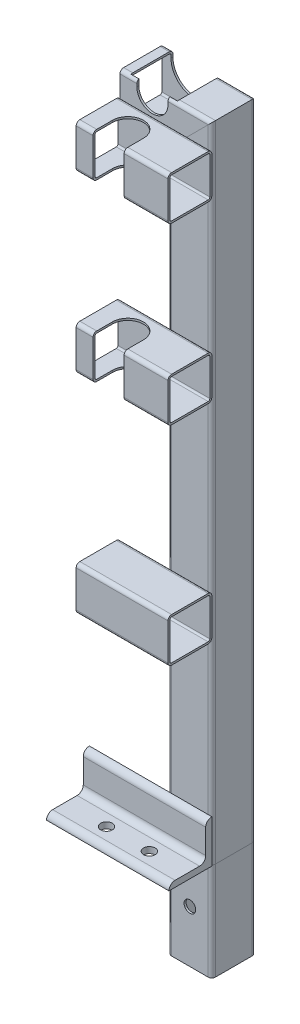
SolidWorks part; units mm, degrees
ref_plane "Front Plane" through (0, 0, 0) normal (0, 0, 1) x (1, 0, 0)
ref_plane "Top Plane" through (0, 0, 0) normal (0, 1, 0) x (1, 0, 0)
ref_plane "Right Plane" through (0, 0, 0) normal (1, 0, 0) x (0, 0, -1)
sketch "Sketch1" plane through (0, 0, 0) normal (0, 0, 1) x (1, 0, 0)
  line L0 (210.6, 0) -> (210.6, 508)
  line L1 (210.6, 508) -> (153.5, 508)
  line L2 (210.6, 0) -> (210.6, -80)
  dimension "D1" = 508
  dimension "D2" = 80
  dimension "D3" = 57.1
  dimension "D4" = 210.6
other "Structural MemberMain"
ref_plane "Plane1" through (210.6, 0, 0) normal (0, 1, 0) x (-1, 0, 0)
sketch "Sketch11" plane through (210.6, 0, 0) normal (0, 1, 0) x (-1, 0, 0)
  line L0 (-14.9, 16.3) -> (14.9, 16.3)
  line L1 (-14.9, 17.9) -> (14.9, 17.9)
  line L2 (-17.9, 14.9) -> (-17.9, -14.9)
  line L3 (-14.9, -17.9) -> (14.9, -17.9)
  line L4 (17.9, 14.9) -> (17.9, -14.9)
  line L5 (-17.9, 17.9) -> (17.9, -17.9) construction
  line L6 (-17.9, -17.9) -> (17.9, 17.9) construction
  line L7 (16.3, 14.9) -> (16.3, -14.9)
  line L8 (-14.9, -16.3) -> (14.9, -16.3)
  line L9 (-16.3, 14.9) -> (-16.3, -14.9)
  arc A0 (-17.9, -14.9) -> (-14.9, -17.9) centre (-14.9, -14.9) ccw
  arc A1 (14.9, -17.9) -> (17.9, -14.9) centre (14.9, -14.9) ccw
  arc A2 (17.9, 14.9) -> (14.9, 17.9) centre (14.9, 14.9) ccw
  arc A3 (-14.9, 17.9) -> (-17.9, 14.9) centre (-14.9, 14.9) ccw
  arc A4 (16.3, 14.9) -> (14.9, 16.3) centre (14.9, 14.9) ccw
  arc A5 (14.9, -16.3) -> (16.3, -14.9) centre (14.9, -14.9) ccw
  arc A6 (-16.3, -14.9) -> (-14.9, -16.3) centre (-14.9, -14.9) ccw
  arc A7 (-14.9, 16.3) -> (-16.3, 14.9) centre (-14.9, 14.9) ccw
  point P0 (0, 0)
  point P30 (0, 0)
  dimension "D3" = 3
  dimension "D1" = 35.8
  dimension "D2" = 35.8
  dimension "D4" = 1.6
sketch "Sketch12" plane through (0, 0, 0) normal (0, 0, 1) x (1, 0, 0)
  line L1 (180, 520.7) -> (180, 531.1) construction
  line L2 (167.3, 520.7) -> (167.3, 531.1)
  line L3 (192.7, 520.7) -> (192.7, 531.1)
  line L4 (210.6, 508) -> (153.5, 508) construction
  line L5 (153.5, 525.9) -> (228.5, 525.9) construction
  arc A0 (167.3, 520.7) -> (192.7, 520.7) centre (180, 520.7) ccw
  arc A1 (192.7, 531.1) -> (167.3, 531.1) centre (180, 531.1) ccw
  point P2 (180, 525.9)
  dimension "D1" = 25.4
  dimension "D2" = 180
extrude "Cut-ExtrudeTopRailGuide" cut sketch "Sketch12" against normal through all and the other way through all
sketch "Sketch13" plane through (0, 0, 0) normal (0, 1, 0) x (1, 0, 0)
  line L0 (128.5, -17.9) -> (228.5, -17.9)
  line L1 (192.7, -17.9) -> (225.5, -17.9) construction
  line L3 (228.5, 14.9) -> (228.5, -14.9) construction
  point P4 (178.5, -17.9)
  dimension "D1" = 100
other "Structural MemberAngle"
ref_plane "Plane2" through (128.5, 0, 17.9) normal (1, 0, 0) x (0, 1, 0)
sketch "Sketch14" plane through (128.5, 0, 17.9) normal (1, 0, 0) x (0, 1, 0)
  line L0 (0, 0) -> (0, 35)
  line L1 (0, 17.5) -> (5, 17.5) construction
  line L2 (5, 30) -> (5, 10)
  line L3 (10, 5) -> (30, 5)
  line L4 (17.5, 5) -> (17.5, 0) construction
  line L5 (35, 0) -> (0, 0)
  arc A0 (35, 0) -> (30, 5) centre (30, 0) ccw
  arc A1 (0, 35) -> (5, 30) centre (0, 30) cw
  arc A2 (10, 5) -> (5, 10) centre (10, 10) cw
  point P10 (17.5, 0)
  point P14 (0, 17.5)
  point P15 (5, 17.5)
  point P16 (17.5, 5)
  point P17 (5, 35)
  point P18 (35, 5)
  point P21 (0, 0)
  dimension "D2" = 5
  dimension "D3" = 35
  dimension "Radius_1" = 5
  dimension "D1" = 5
sketch "Sketch15" plane through (0, 0, 0) normal (0, 1, 0) x (1, 0, 0)
  line L0 (178.5, -17.9) -> (178.5, -52.9) construction
  line L1 (228.5, -52.9) -> (128.5, -52.9) construction
  line L2 (-65.8005, -37.9) -> (422.8005, -37.9) construction
  line L3 (128.5, -17.9) -> (228.5, -17.9) construction
  line L4 (0, 28.933) -> (0, -28.933) construction
  circle A0 centre (162.5, -37.9) radius 4.7625
  circle A1 centre (197.5, -37.9) radius 4.7625
  point P7 (178.5, -37.9)
  point P16 (0, 0)
  dimension "D2" = 9.525
  dimension "D1" = 20
  dimension "D3" = 197.5
  dimension "D4" = 35
extrude "Cut-ExtrudeMountingHoles" cut sketch "Sketch15" along normal through all
sketch "Sketch16" plane through (0, 0, 0) normal (0, 0, 1) x (1, 0, 0)
  line L4 (199.05, 520.7) -> (199.05, 531.1)
  line L5 (160.95, 531.1) -> (160.95, 520.7)
  line L6 (199.05, 520.7) -> (199.05, 531.1)
  line L7 (160.95, 531.1) -> (160.95, 520.7)
  arc A4 (160.95, 520.7) -> (199.05, 520.7) centre (180, 520.7) ccw
  arc A5 (199.05, 531.1) -> (160.95, 531.1) centre (180, 531.1) ccw
  arc A6 (160.95, 520.7) -> (199.05, 520.7) centre (180, 520.7) ccw
  arc A7 (199.05, 531.1) -> (160.95, 531.1) centre (180, 531.1) ccw
  dimension "D1" = 6.35
extrude "Cut-ExtrudeEnlargeRailGuide" cut sketch "Sketch16" against normal through all and the other way up to surface
sketch "Sketch17" plane through (0, 0, 17.9) normal (0, 0, 1) x (1, 0, 0)
  line L0 (228.5, 507) -> (153.5, 507)
  line L1 (228.5, 525.9) -> (228.5, 0) construction
  line L2 (153.5, 493.1) -> (153.5, 522.9) construction
  line L3 (228.5, 194.4) -> (153.5, 194.4)
  line L4 (228.5, 364.4) -> (153.5, 364.4)
  dimension "D1" = 194.4
  dimension "D2" = 312.6
  dimension "D3" = 170
other "Structural Member1"
ref_plane "Plane3" through (228.5, 507, 17.9) normal (-1, 0, 0) x (0, -1, 0)
sketch "Sketch19" plane through (228.5, 489.1, 35.8) normal (-1, 0, 0) x (0, -1, 0)
  line L0 (-14.9, 16.3) -> (14.9, 16.3)
  line L1 (-14.9, 17.9) -> (14.9, 17.9)
  line L2 (-17.9, 14.9) -> (-17.9, -14.9)
  line L3 (-14.9, -17.9) -> (14.9, -17.9)
  line L4 (17.9, 14.9) -> (17.9, -14.9)
  line L5 (-17.9, 17.9) -> (17.9, -17.9) construction
  line L6 (-17.9, -17.9) -> (17.9, 17.9) construction
  line L7 (16.3, 14.9) -> (16.3, -14.9)
  line L8 (-14.9, -16.3) -> (14.9, -16.3)
  line L9 (-16.3, 14.9) -> (-16.3, -14.9)
  arc A0 (-17.9, -14.9) -> (-14.9, -17.9) centre (-14.9, -14.9) ccw
  arc A1 (14.9, -17.9) -> (17.9, -14.9) centre (14.9, -14.9) ccw
  arc A2 (17.9, 14.9) -> (14.9, 17.9) centre (14.9, 14.9) ccw
  arc A3 (-14.9, 17.9) -> (-17.9, 14.9) centre (-14.9, 14.9) ccw
  arc A4 (16.3, 14.9) -> (14.9, 16.3) centre (14.9, 14.9) ccw
  arc A5 (14.9, -16.3) -> (16.3, -14.9) centre (14.9, -14.9) ccw
  arc A6 (-16.3, -14.9) -> (-14.9, -16.3) centre (-14.9, -14.9) ccw
  arc A7 (-14.9, 16.3) -> (-16.3, 14.9) centre (-14.9, 14.9) ccw
  point P0 (0, 0)
  point P30 (0, 0)
  dimension "D3" = 3
  dimension "D1" = 35.8
  dimension "D2" = 35.8
  dimension "D4" = 1.6
sketch "Sketch20" plane through (0, 507, 0) normal (0, 1, 0) x (1, 0, 0)
  line L0 (180, -37.9) -> (180, -70.7688) construction
  line L1 (192.7, -37.9) -> (192.7, -70.7688)
  line L2 (167.3, -37.9) -> (167.3, -70.7688)
  line L3 (128.5, -17.9) -> (228.5, -17.9) construction
  arc A0 (192.7, -37.9) -> (167.3, -37.9) centre (180, -37.9) ccw
  arc A1 (167.3, -70.7688) -> (192.7, -70.7688) centre (180, -70.7688) ccw
  point P2 (180, -54.3344)
  dimension "D1" = 25.4
  dimension "D2" = 180
  dimension "D3" = 20
extrude "Cut-Extrude1" cut sketch "Sketch20" against normal through all
sketch "Sketch21" plane through (0, 0, 17.9) normal (0, 0, 1) x (1, 0, 0)
  line L0 (210.6, 0) -> (210.6, -80) construction
  line L1 (128.5, 0) -> (228.5, 0) construction
  circle A0 centre (210.6, -37.5) radius 4.7625
  dimension "D1" = 9.525
  dimension "D2" = 37.5
extrude "Cut-Extrude2" cut sketch "Sketch21" against normal through all
